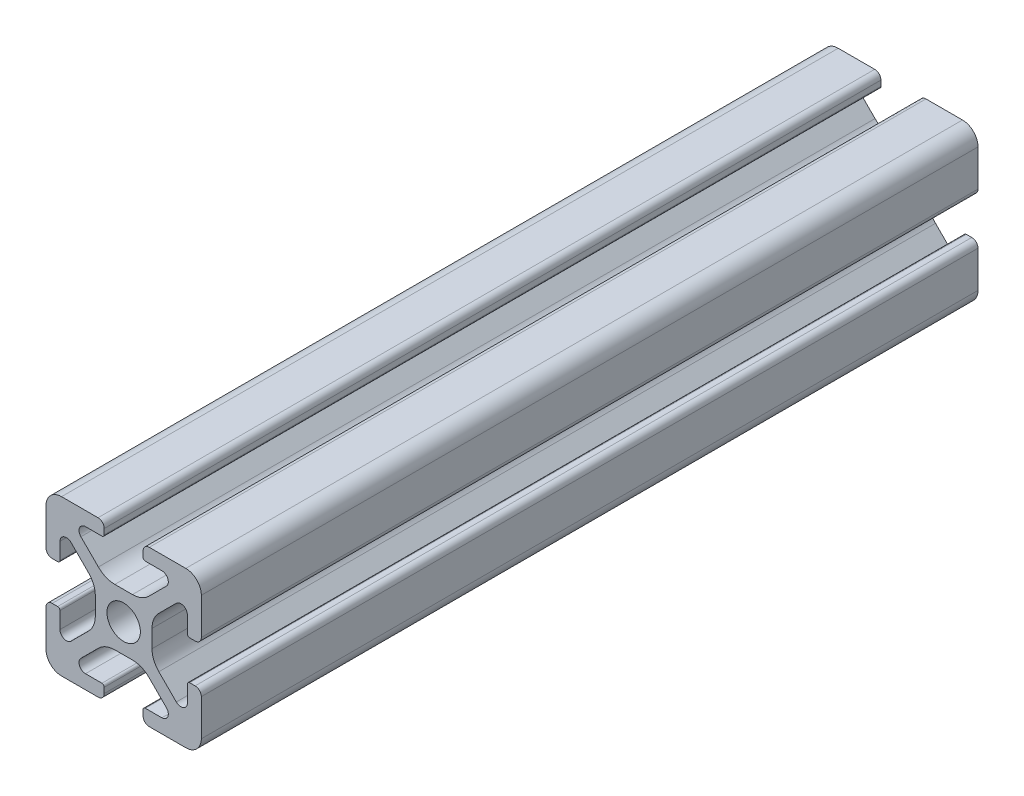
SolidWorks part; units mm, degrees
ref_plane "Front" through (0, 0, 0) normal (0, 0, 1) x (1, 0, 0)
ref_plane "Top" through (0, 0, 0) normal (0, 1, 0) x (1, 0, 0)
ref_plane "Right" through (0, 0, 0) normal (1, 0, 0) x (0, 0, -1)
sketch "Support-Front" plane through (0, 0, 0) normal (0, 0, 1) x (1, 0, 0)
  line L0 (10, 0) -> (-10, 0) construction
  line L1 (-10, -10) -> (10, -10)
  line L2 (-10, -10) -> (-10, 10)
  line L3 (-10, 10) -> (10, 10)
  line L4 (10, -10) -> (10, 10)
  line L5 (0, 10) -> (0, -10) construction
  dimension "Height-Profile" = 20
  dimension "Width-Profile" = 20
sketch "Support-Right-Length" plane through (0, 0, 0) normal (1, 0, 0) x (0, 0, -1)
  line L0 (0, -10) -> (0, 10) construction
  line L1 (-25, 10) -> (25, 10)
  line L2 (-25, 10) -> (-25, -10)
  line L3 (-25, -10) -> (25, -10)
  line L4 (25, 10) -> (25, -10)
  dimension "Length-Profile" = 50
sketch "Support-Profile" plane through (0, 0, 0) normal (0, 0, 1) x (1, 0, 0)
  line L8 (4.9176, -8.2) -> (2.8, -8.2)
  line L9 (2.5, -8.5) -> (2.5, -9.2)
  line L10 (3.3, -10) -> (8, -10)
  line L11 (10, -8) -> (10, -3.3)
  line L24 (9.2, -2.5) -> (8.5, -2.5)
  line L25 (8.2, -2.8) -> (8.2, -4.9176)
  line L26 (6.779, -5.5062) -> (4.5287, -3.2559)
  line L27 (3.65, -1.1346) -> (3.65, 1.1346)
  line L28 (4.5287, 3.2559) -> (6.779, 5.5062)
  line L29 (8.2, 4.9176) -> (8.2, 2.8)
  line L30 (8.5, 2.5) -> (9.2, 2.5)
  line L31 (10, 3.3) -> (10, 8)
  line L32 (8, 10) -> (3.3, 10)
  line L33 (2.5, 9.2) -> (2.5, 8.5)
  line L34 (2.8, 8.2) -> (4.9176, 8.2)
  line L35 (5.5062, 6.779) -> (3.2559, 4.5287)
  line L40 (1.1346, 3.65) -> (-1.1346, 3.65)
  line L41 (-3.2559, 4.5287) -> (-5.5062, 6.779)
  line L42 (-4.9176, 8.2) -> (-2.8, 8.2)
  line L43 (-2.5, 8.5) -> (-2.5, 9.2)
  line L44 (-3.3, 10) -> (-8, 10)
  line L45 (-10, 8) -> (-10, 3.3)
  line L46 (-9.2, 2.5) -> (-8.5, 2.5)
  line L47 (-8.2, 2.8) -> (-8.2, 4.9176)
  line L48 (-6.779, 5.5062) -> (-4.5287, 3.2559)
  line L49 (-3.65, 1.1346) -> (-3.65, -1.1346)
  line L50 (-4.5287, -3.2559) -> (-6.779, -5.5062)
  line L51 (-8.2, -4.9176) -> (-8.2, -2.8)
  line L52 (-8.5, -2.5) -> (-9.2, -2.5)
  line L53 (-10, -3.3) -> (-10, -8)
  line L54 (-8, -10) -> (-3.3, -10)
  line L55 (-2.5, -9.2) -> (-2.5, -8.5)
  line L56 (-2.8, -8.2) -> (-4.9176, -8.2)
  line L57 (-5.5062, -6.779) -> (-3.2559, -4.5287)
  line L58 (-1.1346, -3.65) -> (1.1346, -3.65)
  line L59 (3.2559, -4.5287) -> (5.5062, -6.779)
  circle A2 centre (0, 0) radius 2.15
  arc A3 (2.8, -8.2) -> (2.5, -8.5) centre (2.8, -8.5) ccw
  arc A5 (2.5, -9.2) -> (3.3, -10) centre (3.3, -9.2) ccw
  arc A24 (8, -10) -> (10, -8) centre (8, -8) ccw
  arc A25 (10, -3.3) -> (9.2, -2.5) centre (9.2, -3.3) ccw
  arc A26 (8.5, -2.5) -> (8.2, -2.8) centre (8.5, -2.8) ccw
  arc A27 (6.779, -5.5062) -> (8.2, -4.9176) centre (7.3676, -4.9176) ccw
  arc A28 (3.65, -1.1346) -> (4.5287, -3.2559) centre (6.65, -1.1346) ccw
  arc A29 (4.5287, 3.2559) -> (3.65, 1.1346) centre (6.65, 1.1346) ccw
  arc A30 (8.2, 4.9176) -> (6.779, 5.5062) centre (7.3676, 4.9176) ccw
  arc A31 (8.2, 2.8) -> (8.5, 2.5) centre (8.5, 2.8) ccw
  arc A32 (9.2, 2.5) -> (10, 3.3) centre (9.2, 3.3) ccw
  arc A33 (10, 8) -> (8, 10) centre (8, 8) ccw
  arc A34 (3.3, 10) -> (2.5, 9.2) centre (3.3, 9.2) ccw
  arc A35 (2.5, 8.5) -> (2.8, 8.2) centre (2.8, 8.5) ccw
  arc A38 (5.5062, 6.779) -> (4.9176, 8.2) centre (4.9176, 7.3676) ccw
  arc A39 (1.1346, 3.65) -> (3.2559, 4.5287) centre (1.1346, 6.65) ccw
  arc A44 (-3.2559, 4.5287) -> (-1.1346, 3.65) centre (-1.1346, 6.65) ccw
  arc A45 (-4.9176, 8.2) -> (-5.5062, 6.779) centre (-4.9176, 7.3676) ccw
  arc A46 (-2.8, 8.2) -> (-2.5, 8.5) centre (-2.8, 8.5) ccw
  arc A47 (-2.5, 9.2) -> (-3.3, 10) centre (-3.3, 9.2) ccw
  arc A48 (-8, 10) -> (-10, 8) centre (-8, 8) ccw
  arc A49 (-10, 3.3) -> (-9.2, 2.5) centre (-9.2, 3.3) ccw
  arc A50 (-8.5, 2.5) -> (-8.2, 2.8) centre (-8.5, 2.8) ccw
  arc A51 (-6.779, 5.5062) -> (-8.2, 4.9176) centre (-7.3676, 4.9176) ccw
  arc A52 (-3.65, 1.1346) -> (-4.5287, 3.2559) centre (-6.65, 1.1346) ccw
  arc A53 (-4.5287, -3.2559) -> (-3.65, -1.1346) centre (-6.65, -1.1346) ccw
  arc A54 (-8.2, -4.9176) -> (-6.779, -5.5062) centre (-7.3676, -4.9176) ccw
  arc A55 (-8.2, -2.8) -> (-8.5, -2.5) centre (-8.5, -2.8) ccw
  arc A56 (-9.2, -2.5) -> (-10, -3.3) centre (-9.2, -3.3) ccw
  arc A57 (-10, -8) -> (-8, -10) centre (-8, -8) ccw
  arc A58 (-3.3, -10) -> (-2.5, -9.2) centre (-3.3, -9.2) ccw
  arc A59 (-2.5, -8.5) -> (-2.8, -8.2) centre (-2.8, -8.5) ccw
  arc A60 (-5.5062, -6.779) -> (-4.9176, -8.2) centre (-4.9176, -7.3676) ccw
  arc A61 (-1.1346, -3.65) -> (-3.2559, -4.5287) centre (-1.1346, -6.65) ccw
  arc A62 (3.2559, -4.5287) -> (1.1346, -3.65) centre (1.1346, -6.65) ccw
  arc A63 (4.9176, -8.2) -> (5.5062, -6.779) centre (4.9176, -7.3676) ccw
ref_plane "Ref-Plane-1" through (0, 0, 25) normal (0, 0, 1) x (1, 0, 0)
ref_plane "Ref-Plane-2" through (0, 0, -25) normal (0, 0, 1) x (1, 0, 0)
sketch "Sketch4" plane through (0, 0, 25) normal (0, 0, 1) x (1, 0, 0)
  line L0 (-10, -10) -> (-10, 10) construction
  line L1 (-10, -10) -> (10, -10) construction
  line L2 (10, -10) -> (10, 10) construction
  line L3 (-10, 10) -> (10, 10) construction
  line L4 (-10, -10) -> (-10, 10)
  line L5 (-10, -10) -> (10, -10)
  line L6 (10, -10) -> (10, 10)
  line L7 (-10, 10) -> (10, 10)
extrude "Body" add sketch "Sketch4" against normal blind 100
sketch "Sketch16" plane through (0, 0, 0) normal (0, 0, 1) x (1, 0, 0)
  line L40 (4.9176, -8.2) -> (2.8, -8.2)
  line L41 (2.5, -8.5) -> (2.5, -9.2)
  line L42 (3.3, -10) -> (8, -10)
  line L43 (10, -8) -> (10, -3.3)
  line L44 (9.2, -2.5) -> (8.5, -2.5)
  line L45 (8.2, -2.8) -> (8.2, -4.9176)
  line L46 (6.779, -5.5062) -> (4.5287, -3.2559)
  line L47 (3.65, -1.1346) -> (3.65, 1.1346)
  line L48 (4.5287, 3.2559) -> (6.779, 5.5062)
  line L49 (8.2, 4.9176) -> (8.2, 2.8)
  line L50 (8.5, 2.5) -> (9.2, 2.5)
  line L51 (10, 3.3) -> (10, 8)
  line L52 (8, 10) -> (3.3, 10)
  line L53 (2.5, 9.2) -> (2.5, 8.5)
  line L54 (2.8, 8.2) -> (4.9176, 8.2)
  line L55 (5.5062, 6.779) -> (3.2559, 4.5287)
  line L56 (1.1346, 3.65) -> (-1.1346, 3.65)
  line L57 (-3.2559, 4.5287) -> (-5.5062, 6.779)
  line L58 (-4.9176, 8.2) -> (-2.8, 8.2)
  line L59 (-2.5, 8.5) -> (-2.5, 9.2)
  line L60 (-3.3, 10) -> (-8, 10)
  line L61 (-10, 8) -> (-10, 3.3)
  line L62 (-9.2, 2.5) -> (-8.5, 2.5)
  line L63 (-8.2, 2.8) -> (-8.2, 4.9176)
  line L64 (-6.779, 5.5062) -> (-4.5287, 3.2559)
  line L65 (-3.65, 1.1346) -> (-3.65, -1.1346)
  line L66 (-4.5287, -3.2559) -> (-6.779, -5.5062)
  line L67 (-8.2, -4.9176) -> (-8.2, -2.8)
  line L68 (-8.5, -2.5) -> (-9.2, -2.5)
  line L69 (-10, -3.3) -> (-10, -8)
  line L70 (-8, -10) -> (-3.3, -10)
  line L71 (-2.5, -9.2) -> (-2.5, -8.5)
  line L72 (-2.8, -8.2) -> (-4.9176, -8.2)
  line L73 (-5.5062, -6.779) -> (-3.2559, -4.5287)
  line L74 (-1.1346, -3.65) -> (1.1346, -3.65)
  line L75 (3.2559, -4.5287) -> (5.5062, -6.779)
  line L76 (4.9176, -8.2) -> (2.8, -8.2)
  line L77 (2.5, -8.5) -> (2.5, -9.2)
  line L78 (3.3, -10) -> (8, -10)
  line L79 (10, -8) -> (10, -3.3)
  line L80 (9.2, -2.5) -> (8.5, -2.5)
  line L81 (8.2, -2.8) -> (8.2, -4.9176)
  line L82 (6.779, -5.5062) -> (4.5287, -3.2559)
  line L83 (3.65, -1.1346) -> (3.65, 1.1346)
  line L84 (4.5287, 3.2559) -> (6.779, 5.5062)
  line L85 (8.2, 4.9176) -> (8.2, 2.8)
  line L86 (8.5, 2.5) -> (9.2, 2.5)
  line L87 (10, 3.3) -> (10, 8)
  line L88 (8, 10) -> (3.3, 10)
  line L89 (2.5, 9.2) -> (2.5, 8.5)
  line L90 (2.8, 8.2) -> (4.9176, 8.2)
  line L91 (5.5062, 6.779) -> (3.2559, 4.5287)
  line L92 (1.1346, 3.65) -> (-1.1346, 3.65)
  line L93 (-3.2559, 4.5287) -> (-5.5062, 6.779)
  line L94 (-4.9176, 8.2) -> (-2.8, 8.2)
  line L95 (-2.5, 8.5) -> (-2.5, 9.2)
  line L96 (-3.3, 10) -> (-8, 10)
  line L97 (-10, 8) -> (-10, 3.3)
  line L98 (-9.2, 2.5) -> (-8.5, 2.5)
  line L99 (-8.2, 2.8) -> (-8.2, 4.9176)
  line L100 (-6.779, 5.5062) -> (-4.5287, 3.2559)
  line L101 (-3.65, 1.1346) -> (-3.65, -1.1346)
  line L102 (-4.5287, -3.2559) -> (-6.779, -5.5062)
  line L103 (-8.2, -4.9176) -> (-8.2, -2.8)
  line L104 (-8.5, -2.5) -> (-9.2, -2.5)
  line L105 (-10, -3.3) -> (-10, -8)
  line L106 (-8, -10) -> (-3.3, -10)
  line L107 (-2.5, -9.2) -> (-2.5, -8.5)
  line L108 (-2.8, -8.2) -> (-4.9176, -8.2)
  line L109 (-5.5062, -6.779) -> (-3.2559, -4.5287)
  line L110 (-1.1346, -3.65) -> (1.1346, -3.65)
  line L111 (3.2559, -4.5287) -> (5.5062, -6.779)
  circle A7 centre (0, 0) radius 2.15 construction
  circle A8 centre (0, 0) radius 2.15
  arc A43 (2.8, -8.2) -> (2.5, -8.5) centre (2.8, -8.5) ccw
  arc A44 (2.5, -9.2) -> (3.3, -10) centre (3.3, -9.2) ccw
  arc A45 (8, -10) -> (10, -8) centre (8, -8) ccw
  arc A46 (10, -3.3) -> (9.2, -2.5) centre (9.2, -3.3) ccw
  arc A47 (8.5, -2.5) -> (8.2, -2.8) centre (8.5, -2.8) ccw
  arc A48 (6.779, -5.5062) -> (8.2, -4.9176) centre (7.3676, -4.9176) ccw
  arc A49 (3.65, -1.1346) -> (4.5287, -3.2559) centre (6.65, -1.1346) ccw
  arc A50 (4.5287, 3.2559) -> (3.65, 1.1346) centre (6.65, 1.1346) ccw
  arc A51 (8.2, 4.9176) -> (6.779, 5.5062) centre (7.3676, 4.9176) ccw
  arc A52 (8.2, 2.8) -> (8.5, 2.5) centre (8.5, 2.8) ccw
  arc A53 (9.2, 2.5) -> (10, 3.3) centre (9.2, 3.3) ccw
  arc A54 (10, 8) -> (8, 10) centre (8, 8) ccw
  arc A55 (3.3, 10) -> (2.5, 9.2) centre (3.3, 9.2) ccw
  arc A56 (2.5, 8.5) -> (2.8, 8.2) centre (2.8, 8.5) ccw
  arc A57 (5.5062, 6.779) -> (4.9176, 8.2) centre (4.9176, 7.3676) ccw
  arc A58 (1.1346, 3.65) -> (3.2559, 4.5287) centre (1.1346, 6.65) ccw
  arc A59 (-3.2559, 4.5287) -> (-1.1346, 3.65) centre (-1.1346, 6.65) ccw
  arc A60 (-4.9176, 8.2) -> (-5.5062, 6.779) centre (-4.9176, 7.3676) ccw
  arc A61 (-2.8, 8.2) -> (-2.5, 8.5) centre (-2.8, 8.5) ccw
  arc A62 (-2.5, 9.2) -> (-3.3, 10) centre (-3.3, 9.2) ccw
  arc A63 (-8, 10) -> (-10, 8) centre (-8, 8) ccw
  arc A64 (-10, 3.3) -> (-9.2, 2.5) centre (-9.2, 3.3) ccw
  arc A65 (-8.5, 2.5) -> (-8.2, 2.8) centre (-8.5, 2.8) ccw
  arc A66 (-6.779, 5.5062) -> (-8.2, 4.9176) centre (-7.3676, 4.9176) ccw
  arc A67 (-3.65, 1.1346) -> (-4.5287, 3.2559) centre (-6.65, 1.1346) ccw
  arc A68 (-4.5287, -3.2559) -> (-3.65, -1.1346) centre (-6.65, -1.1346) ccw
  arc A69 (-8.2, -4.9176) -> (-6.779, -5.5062) centre (-7.3676, -4.9176) ccw
  arc A70 (-8.2, -2.8) -> (-8.5, -2.5) centre (-8.5, -2.8) ccw
  arc A71 (-9.2, -2.5) -> (-10, -3.3) centre (-9.2, -3.3) ccw
  arc A72 (-10, -8) -> (-8, -10) centre (-8, -8) ccw
  arc A73 (-3.3, -10) -> (-2.5, -9.2) centre (-3.3, -9.2) ccw
  arc A74 (-2.5, -8.5) -> (-2.8, -8.2) centre (-2.8, -8.5) ccw
  arc A75 (-5.5062, -6.779) -> (-4.9176, -8.2) centre (-4.9176, -7.3676) ccw
  arc A76 (-1.1346, -3.65) -> (-3.2559, -4.5287) centre (-1.1346, -6.65) ccw
  arc A77 (3.2559, -4.5287) -> (1.1346, -3.65) centre (1.1346, -6.65) ccw
  arc A78 (4.9176, -8.2) -> (5.5062, -6.779) centre (4.9176, -7.3676) ccw
  arc A79 (2.8, -8.2) -> (2.5, -8.5) centre (2.8, -8.5) ccw
  arc A80 (2.5, -9.2) -> (3.3, -10) centre (3.3, -9.2) ccw
  arc A81 (8, -10) -> (10, -8) centre (8, -8) ccw
  arc A82 (10, -3.3) -> (9.2, -2.5) centre (9.2, -3.3) ccw
  arc A83 (8.5, -2.5) -> (8.2, -2.8) centre (8.5, -2.8) ccw
  arc A84 (6.779, -5.5062) -> (8.2, -4.9176) centre (7.3676, -4.9176) ccw
  arc A85 (3.65, -1.1346) -> (4.5287, -3.2559) centre (6.65, -1.1346) ccw
  arc A86 (4.5287, 3.2559) -> (3.65, 1.1346) centre (6.65, 1.1346) ccw
  arc A87 (8.2, 4.9176) -> (6.779, 5.5062) centre (7.3676, 4.9176) ccw
  arc A88 (8.2, 2.8) -> (8.5, 2.5) centre (8.5, 2.8) ccw
  arc A89 (9.2, 2.5) -> (10, 3.3) centre (9.2, 3.3) ccw
  arc A90 (10, 8) -> (8, 10) centre (8, 8) ccw
  arc A91 (3.3, 10) -> (2.5, 9.2) centre (3.3, 9.2) ccw
  arc A92 (2.5, 8.5) -> (2.8, 8.2) centre (2.8, 8.5) ccw
  arc A93 (5.5062, 6.779) -> (4.9176, 8.2) centre (4.9176, 7.3676) ccw
  arc A94 (1.1346, 3.65) -> (3.2559, 4.5287) centre (1.1346, 6.65) ccw
  arc A95 (-3.2559, 4.5287) -> (-1.1346, 3.65) centre (-1.1346, 6.65) ccw
  arc A96 (-4.9176, 8.2) -> (-5.5062, 6.779) centre (-4.9176, 7.3676) ccw
  arc A97 (-2.8, 8.2) -> (-2.5, 8.5) centre (-2.8, 8.5) ccw
  arc A98 (-2.5, 9.2) -> (-3.3, 10) centre (-3.3, 9.2) ccw
  arc A99 (-8, 10) -> (-10, 8) centre (-8, 8) ccw
  arc A100 (-10, 3.3) -> (-9.2, 2.5) centre (-9.2, 3.3) ccw
  arc A101 (-8.5, 2.5) -> (-8.2, 2.8) centre (-8.5, 2.8) ccw
  arc A102 (-6.779, 5.5062) -> (-8.2, 4.9176) centre (-7.3676, 4.9176) ccw
  arc A103 (-3.65, 1.1346) -> (-4.5287, 3.2559) centre (-6.65, 1.1346) ccw
  arc A104 (-4.5287, -3.2559) -> (-3.65, -1.1346) centre (-6.65, -1.1346) ccw
  arc A105 (-8.2, -4.9176) -> (-6.779, -5.5062) centre (-7.3676, -4.9176) ccw
  arc A106 (-8.2, -2.8) -> (-8.5, -2.5) centre (-8.5, -2.8) ccw
  arc A107 (-9.2, -2.5) -> (-10, -3.3) centre (-9.2, -3.3) ccw
  arc A108 (-10, -8) -> (-8, -10) centre (-8, -8) ccw
  arc A109 (-3.3, -10) -> (-2.5, -9.2) centre (-3.3, -9.2) ccw
  arc A110 (-2.5, -8.5) -> (-2.8, -8.2) centre (-2.8, -8.5) ccw
  arc A111 (-5.5062, -6.779) -> (-4.9176, -8.2) centre (-4.9176, -7.3676) ccw
  arc A112 (-1.1346, -3.65) -> (-3.2559, -4.5287) centre (-1.1346, -6.65) ccw
  arc A113 (3.2559, -4.5287) -> (1.1346, -3.65) centre (1.1346, -6.65) ccw
  arc A114 (4.9176, -8.2) -> (5.5062, -6.779) centre (4.9176, -7.3676) ccw
  dimension "D1" = 0
extrude "Cut-Profile" cut sketch "Sketch16" against normal through all and the other way through all flip side to cut
